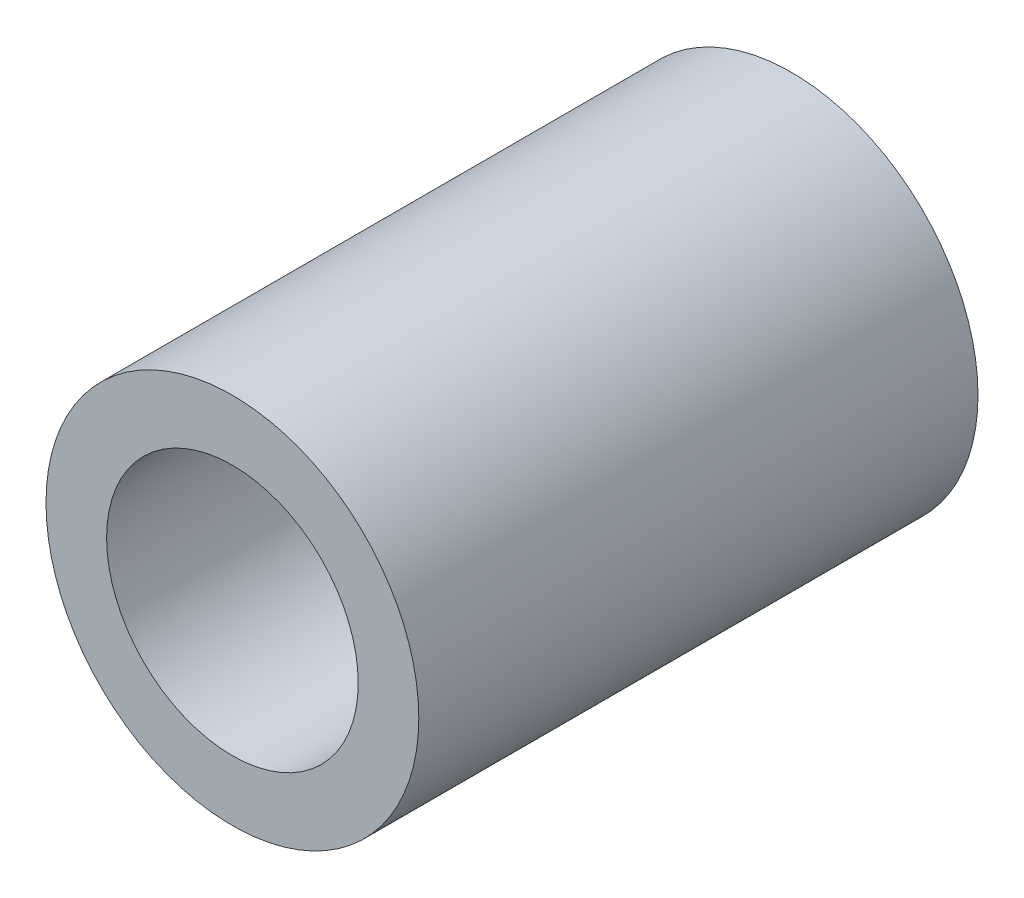
SolidWorks part; units mm, degrees
ref_plane "Alzado" through (0, 0, 0) normal (0, 0, 1) x (1, 0, 0)
ref_plane "Planta" through (0, 0, 0) normal (0, 1, 0) x (1, 0, 0)
ref_plane "Vista lateral" through (0, 0, 0) normal (1, 0, 0) x (0, 0, -1)
sketch "Croquis1" plane through (0, 0, 0) normal (0, 0, 1) x (1, 0, 0)
  circle A0 centre (0, 0) radius 2
  circle A1 centre (0, 0) radius 1.35
extrude "Saliente-Extruir1" add sketch "Croquis1" along normal blind 6
